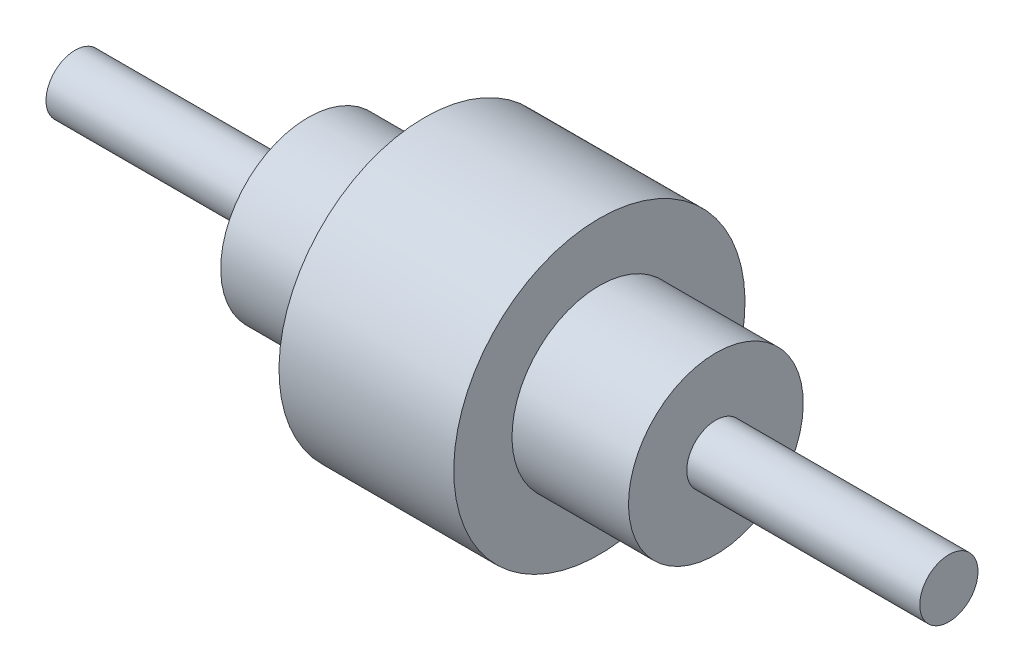
SolidWorks part; units mm, degrees
ref_plane "Front Plane" through (0, 0, 0) normal (0, 0, 1) x (1, 0, 0)
ref_plane "Top Plane" through (0, 0, 0) normal (0, 1, 0) x (1, 0, 0)
ref_plane "Right Plane" through (0, 0, 0) normal (1, 0, 0) x (0, 0, -1)
sketch "Sketch1" plane through (0, 0, 0) normal (0, 0, 1) x (1, 0, 0)
  line L0 (0, 0) -> (127.719, 0) construction
  line L1 (0, 0) -> (-147.426, 0) construction
  line L2 (-30, 30) -> (-30, 50)
  line L3 (-30, 50) -> (30, 50)
  line L4 (-30, 30) -> (-70, 30)
  line L5 (-70, 30) -> (-70, 10)
  line L6 (-70, 10) -> (-150, 10)
  line L7 (-150, 10) -> (-150, 0)
  line L8 (30, 50) -> (30, 30)
  line L9 (30, 30) -> (70, 30)
  line L10 (70, 30) -> (70, 10)
  line L11 (70, 10) -> (150, 10)
  line L12 (150, 10) -> (150, 0)
  line L13 (127.719, 0) -> (202.3465, 0) construction
  line L14 (150, 0) -> (-150, 0)
  dimension "D1" = 60
  dimension "D2" = 20
  dimension "D3" = 60
  dimension "D4" = 100
  dimension "D5" = 40
  dimension "D6" = 80
  dimension "D7" = 30
revolve "Revolve1" add sketch "Sketch1" angle 360 about L14
